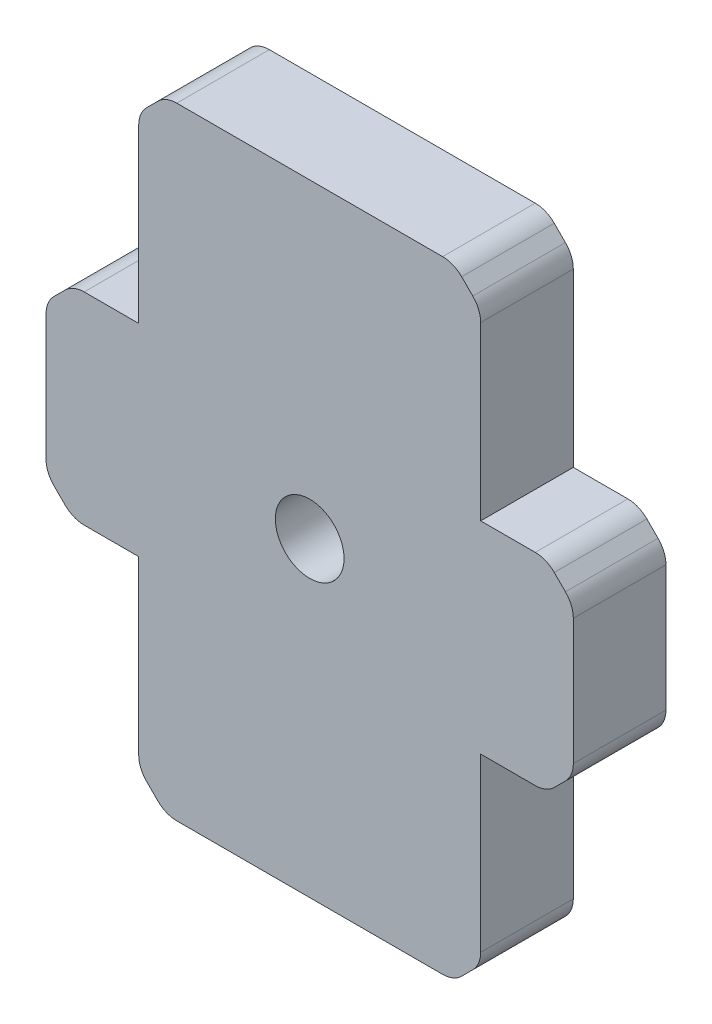
SolidWorks part; units mm, degrees
ref_plane "Front Plane" through (0, 0, 0) normal (0, 0, 1) x (1, 0, 0)
ref_plane "Top Plane" through (0, 0, 0) normal (0, 1, 0) x (1, 0, 0)
ref_plane "Right Plane" through (0, 0, 0) normal (1, 0, 0) x (0, 0, -1)
sketch "Sketch1" plane through (0, 0, 0) normal (0, 0, 1) x (1, 0, 0)
  line L1 (12.7, -23.082) -> (-12.7, -23.082)
  line L2 (12.7, -23.082) -> (12.7, 23.082)
  line L3 (12.7, 23.082) -> (-12.7, 23.082)
  line L4 (-12.7, -23.082) -> (-12.7, 23.082)
  line L5 (12.7, -23.082) -> (-12.7, 23.082) construction
  line L6 (12.7, 23.082) -> (-12.7, -23.082) construction
  point P0 (0, 0)
  dimension "D1" = 46.164
  dimension "D2" = 25.4
extrude "Boss-Extrude1" add sketch "Sketch1" against normal blind 6.88
sketch "Sketch2" plane through (0, 0, 0) normal (0, 0, 1) x (1, 0, 0)
  line L0 (-12.7, 23.082) -> (-12.7, -23.082) construction
  line L1 (-5.82, -7.5) -> (-19.58, -7.5)
  line L2 (-5.82, -7.5) -> (-5.82, 7.5)
  line L3 (-5.82, 7.5) -> (-19.58, 7.5)
  line L4 (-19.58, -7.5) -> (-19.58, 7.5)
  line L5 (-5.82, -7.5) -> (-19.58, 7.5) construction
  line L6 (-5.82, 7.5) -> (-19.58, -7.5) construction
  point P0 (-12.7, 0)
  dimension "D1" = 6.88
  dimension "D2" = 15
extrude "Boss-Extrude2" add sketch "Sketch2" against normal up to vertex (6.88 mm away)
mirror "Mirror2" about plane through (0, 0, 0) normal (1, 0, 0) of "Boss-Extrude2"
sketch "Sketch3" plane through (0, 0, 0) normal (0, 0, 1) x (1, 0, 0)
  circle A0 centre (0, 0) radius 2.55
  dimension "D1" = 5.1
extrude "Cut-Extrude1" cut sketch "Sketch3" against normal through all
chamfer "Chamfer1" distance 2 angle 45 8 edges at (-12.7, 23.082, -3.44) (-19.58, 7.5, -3.44) (-19.58, -7.5, -3.44) (-12.7, -23.082, -3.44) (12.7, -23.082, -3.44) (19.58, -7.5, -3.44) (12.7, 23.082, -3.44) (19.58, 7.5, -3.44)
fillet "Fillet1" radius 2 16 edges at (10.7, 23.082, -3.44) (12.7, 21.082, -3.44) (17.58, 7.5, -3.44) (19.58, 5.5, -3.44) (19.58, -5.5, -3.44) (17.58, -7.5, -3.44) (-19.58, -5.5, -3.44) (-19.58, 5.5, -3.44) (-17.58, 7.5, -3.44) (-12.7, 21.082, -3.44) (-10.7, 23.082, -3.44) (-17.58, -7.5, -3.44) (-12.7, -21.082, -3.44) (-10.7, -23.082, -3.44) (10.7, -23.082, -3.44) (12.7, -21.082, -3.44)
